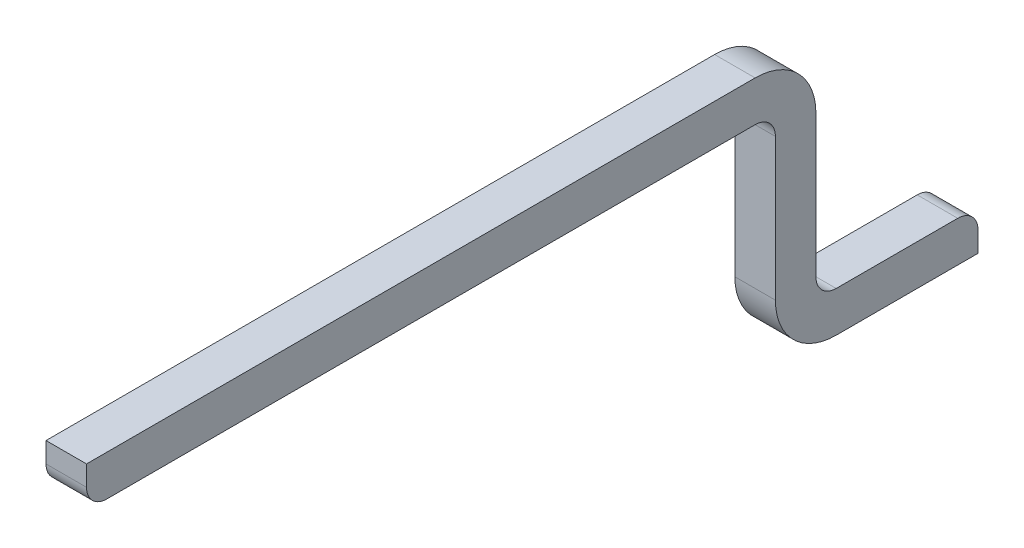
SolidWorks part; units mm, degrees
material "Pure Gold"
ref_plane "Front Plane" through (0, 0, 0) normal (0, 0, 1) x (1, 0, 0)
ref_plane "Top Plane" through (0, 0, 0) normal (0, 1, 0) x (1, 0, 0)
ref_plane "Right Plane" through (0, 0, 0) normal (1, 0, 0) x (0, 0, -1)
sketch "Sketch1" plane through (0, 0, 0) normal (1, 0, 0) x (0, 0, -1)
  line L0 (0.8, 1.1) -> (4.1, 1.1)
  line L2 (4.2, 1) -> (4.2, 0.3)
  line L3 (4.5, 0) -> (5.2, 0)
  line L5 (0.11, 0) -> (-0.11, 0) construction
  line L7 (0, 0.11) -> (0, -0.11) construction
  line L8 (3.5, 1.1) -> (3.5, 0) construction
  arc A0 (4.1, 1.1) -> (4.2, 1) centre (4.1, 1) cw
  arc A1 (4.2, 0.3) -> (4.5, 0) centre (4.5, 0.3) ccw
  dimension "D6" = 0.1
  dimension "D7" = 0.3
  dimension "D1" = 1.1
  dimension "D2" = 0.8
  dimension "D3" = 5.2
  dimension "D4" = 3.5
  dimension "D5" = 0.7
extrude "Extrude-Thin1" add sketch "Sketch1" along normal mid plane 0.2 thin thin type one direction reverse wall 0.2
fillet "Fillet1" radius 0.1 2 edges at (0, 0.2, -5.2) (0, 1.1, -0.8)
